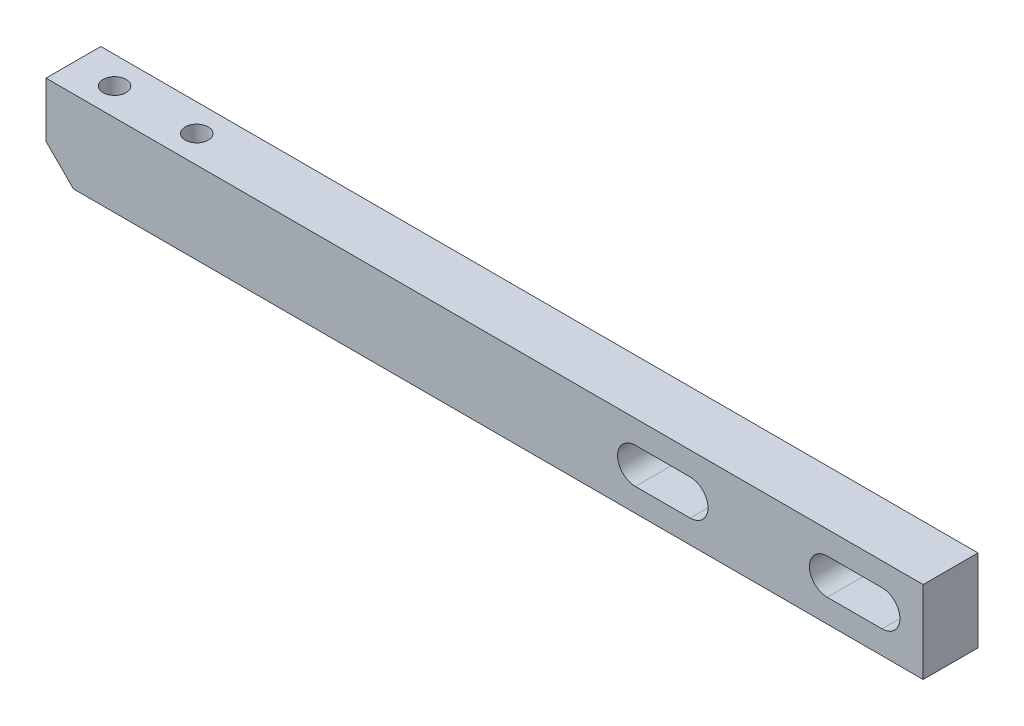
SolidWorks part; units mm, degrees
material "A3钢"
ref_plane "前视基准面" through (0, 0, 0) normal (0, 0, 1) x (1, 0, 0)
ref_plane "上视基准面" through (0, 0, 0) normal (0, 1, 0) x (1, 0, 0)
ref_plane "右视基准面" through (0, 0, 0) normal (1, 0, 0) x (0, 0, -1)
sketch "草图1" plane through (0, 0, 0) normal (0, 0, 1) x (1, 0, 0)
  line L0 (-90.752, 0) -> (79.5928, 0) construction
  line L1 (0, 45.6897) -> (0, -48.7931) construction
  line L3 (0, 0) -> (160, 0)
  line L4 (0, 0) -> (0, 15)
  line L5 (0, 15) -> (160, 15)
  line L6 (160, 0) -> (160, 15)
  dimension "D1" = 15
  dimension "D2" = 160
extrude "凸台-拉伸1" add sketch "草图1" along normal blind 10
sketch "草图2" plane through (0, 15, 0) normal (0, 1, 0) x (1, 0, 0)
  line L0 (0, -5) -> (30, -5) construction
  line L1 (0, -10) -> (0, 0) construction
  circle A0 centre (22.5, -5) radius 2.5
  circle A1 centre (7.5, -5) radius 2.5
  dimension "D1" = 15
  dimension "D3" = 7.5
  dimension "D4" = 5
  dimension "D2" = 30
hole_wizard "M5 螺纹孔1" positions "3D草图1" profile "草图3" tap size "M5" standard "GB"
sketch3d "3D草图1"
  point P0 (7.5, 15, 5)
  point P3 (22.5, 15, 5)
sketch "草图3" plane through (7.5, 15, 5) normal (1, 0, 0) x (0, 0, 1)
  line L0 (0, 0) -> (0, 14.2618)
  line L1 (0, 14.2618) -> (2.1, 13)
  line L2 (2.1, 13) -> (2.1, 0)
  line L5 (2.1, 0) -> (0, 0)
  line L10 (0, 14.2618) -> (-2.1, 13) construction
  line L11 (0, -6.35) -> (0, 107.95) construction
  dimension "螺纹孔钻头直径" = 4.2
  dimension "螺纹孔钻头深度" = 13
  dimension "导头角度" = 118
cosmetic thread "孔螺蚊线3" parameters "D1"=10, "D2"=5
cosmetic thread "孔螺蚊线4" parameters "D1"=10, "D2"=5
chamfer "倒角1" distance 5 angle 45 1 edges at (0, 0, 5)
sketch "草图4" plane through (0, 0, 0) normal (0, 0, -1) x (-1, 0, 0)
  line L0 (-160, 7.5) -> (-100, 7.5) construction
  line L1 (-160, 0) -> (-160, 15) construction
  line L2 (-130, 7.5) -> (-130, 0) construction
  line L3 (-5, 0) -> (-160, 0) construction
  line L4 (-152.5, 7.5) -> (-142.5, 7.5) construction
  line L5 (-152.5, 10.75) -> (-142.5, 10.75)
  line L6 (-152.5, 4.25) -> (-142.5, 4.25)
  line L7 (-117.5, 7.5) -> (-107.5, 7.5) construction
  line L8 (-117.5, 10.75) -> (-107.5, 10.75)
  line L9 (-117.5, 4.25) -> (-107.5, 4.25)
  arc A0 (-152.5, 10.75) -> (-152.5, 4.25) centre (-152.5, 7.5) ccw
  arc A1 (-142.5, 4.25) -> (-142.5, 10.75) centre (-142.5, 7.5) ccw
  arc A2 (-117.5, 10.75) -> (-117.5, 4.25) centre (-117.5, 7.5) ccw
  arc A3 (-107.5, 4.25) -> (-107.5, 10.75) centre (-107.5, 7.5) ccw
  point P10 (-147.5, 7.5)
  point P16 (-112.5, 7.5)
  dimension "D5" = 3.25
  dimension "D7" = 3.25
  dimension "D1" = 60
  dimension "D2" = 10
  dimension "D3" = 10
  dimension "D4" = 17.5
  dimension "D6" = 17.5
extrude "切除-拉伸1" cut sketch "草图4" against normal blind 10
